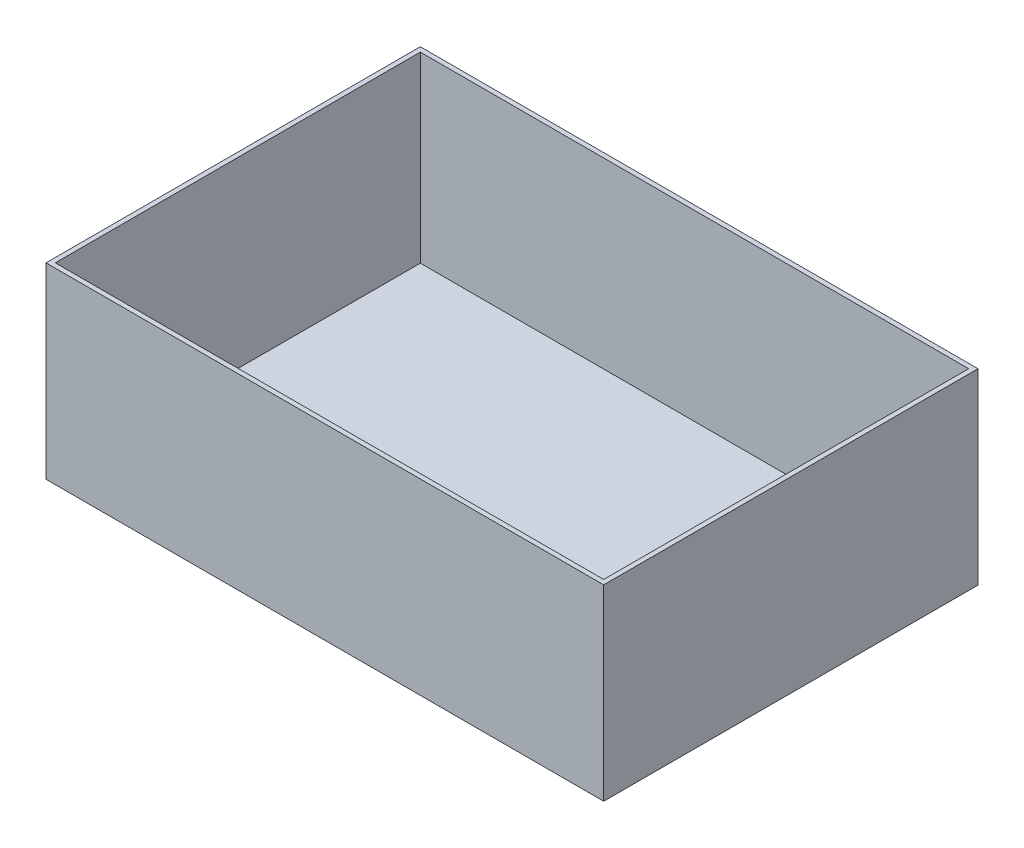
SolidWorks part; units mm, degrees
ref_plane "Front Plane" through (0, 0, 0) normal (0, 0, 1) x (1, 0, 0)
ref_plane "Top Plane" through (0, 0, 0) normal (0, 1, 0) x (1, 0, 0)
ref_plane "Right Plane" through (0, 0, 0) normal (1, 0, 0) x (0, 0, -1)
sketch "Sketch2" plane through (0, 0, 0) normal (0, 1, 0) x (1, 0, 0)
  line L1 (0, 0) -> (600, 0)
  line L2 (0, 0) -> (0, 399.38)
  line L3 (0, 399.38) -> (600, 399.38)
  line L4 (600, 0) -> (600, 399.38)
  dimension "D1" = 600
  dimension "D2" = 399.38
extrude "Boss-Extrude1" add sketch "Sketch2" along normal blind 200
shell "Shell1" thickness 5.08
